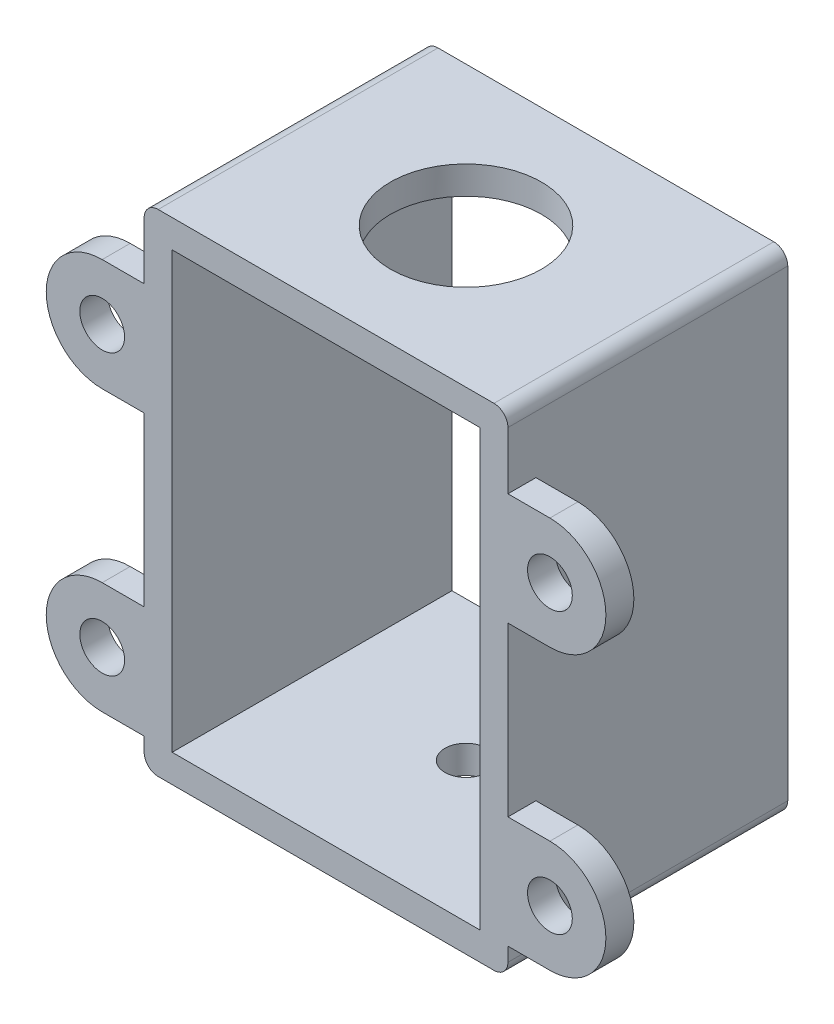
SolidWorks part; units mm, degrees
ref_plane "Front" through (0, 0, 0) normal (0, 0, 1) x (1, 0, 0)
ref_plane "Top" through (0, 0, 0) normal (0, 1, 0) x (1, 0, 0)
ref_plane "Right" through (0, 0, 0) normal (1, 0, 0) x (0, 0, -1)
sketch "Sketch1" plane through (0, 0, 0) normal (0, 0, 1) x (1, 0, 0)
  line L0 (0, 0) -> (22, 0)
  line L1 (22, 0) -> (22, -31.5)
  line L2 (22, -31.5) -> (0, -31.5)
  line L3 (0, -31.5) -> (0, 0)
  line L5 (22, 2) -> (24, 2)
  line L6 (24, 2) -> (24, -33.5)
  line L7 (24, -33.5) -> (-2, -33.5)
  line L8 (-2, -33.5) -> (-2, 2)
  line L9 (-2, 2) -> (22, 2)
extrude "Boss-Extrude1" add sketch "Sketch1" along normal blind 20
sketch "Sketch2" plane through (0, 2, 0) normal (0, 1, 0) x (1, 0, 0)
  circle A0 centre (11, -10) radius 5.4
extrude "Cut-Extrude1" cut sketch "Sketch2" against normal blind 20
sketch "Sketch3" plane through (0, -33.5, 0) normal (0, -1, 0) x (-1, 0, 0)
  circle A0 centre (-11, -10) radius 1.5
extrude "Cut-Extrude2" cut sketch "Sketch3" against normal blind 20
sketch "Sketch4" plane through (0, -31.5, 0) normal (0, 1, 0) x (1, 0, 0)
  line L0 (22, -20) -> (22, 0)
  line L1 (22, 0) -> (0, 0)
  line L2 (0, 0) -> (0, -20)
  line L3 (0, -20) -> (22, -20)
  circle A0 centre (11, -10) radius 1.5
extrude "Boss-Extrude2" add sketch "Sketch4" along normal blind 0.4
sketch "Sketch5" plane through (0, -33.5, 0) normal (0, -1, 0) x (-1, 0, 0)
  circle A0 centre (-11, -10) radius 44.087
extrude "Cut-Extrude3" cut sketch "Sketch5" against normal blind 0.4
fillet "Fillet2" radius 1 4 edges at (24, -33.1, 10) (24, 2, 10) (-2, 2, 10) (-2, -33.1, 10)
sketch "Sketch6" plane through (0, 0, 20) normal (0, 0, 1) x (1, 0, 0)
  line L0 (22, -31.1) -> (27, -31.1)
  line L2 (27, -23.1) -> (22, -23.1)
  line L3 (22, -31.1) -> (22, 0) construction
  line L4 (22, -23.1) -> (22, -31.1)
  line L5 (27, -11.1) -> (22, -11.1)
  line L6 (22, -11.1) -> (22, -3.1)
  line L7 (22, -3.1) -> (27, -3.1)
  line L9 (0, -3.1) -> (-5, -3.1)
  line L10 (0, -11.1) -> (0, -3.1)
  line L11 (-5, -11.1) -> (0, -11.1)
  line L12 (0, -23.1) -> (0, -31.1)
  line L13 (-5, -23.1) -> (0, -23.1)
  line L14 (0, -31.1) -> (-5, -31.1)
  arc A0 (27, -31.1) -> (27, -23.1) centre (27, -27.1) ccw
  circle A1 centre (27, -27.1) radius 1.6
  circle A2 centre (27, -7.1) radius 1.6
  arc A3 (27, -11.1) -> (27, -3.1) centre (27, -7.1) ccw
  arc A4 (-5, -11.1) -> (-5, -3.1) centre (-5, -7.1) cw
  circle A5 centre (-5, -7.1) radius 1.6
  circle A6 centre (-5, -27.1) radius 1.6
  arc A7 (-5, -31.1) -> (-5, -23.1) centre (-5, -27.1) cw
extrude "Boss-Extrude3" add sketch "Sketch6" against normal blind 2
